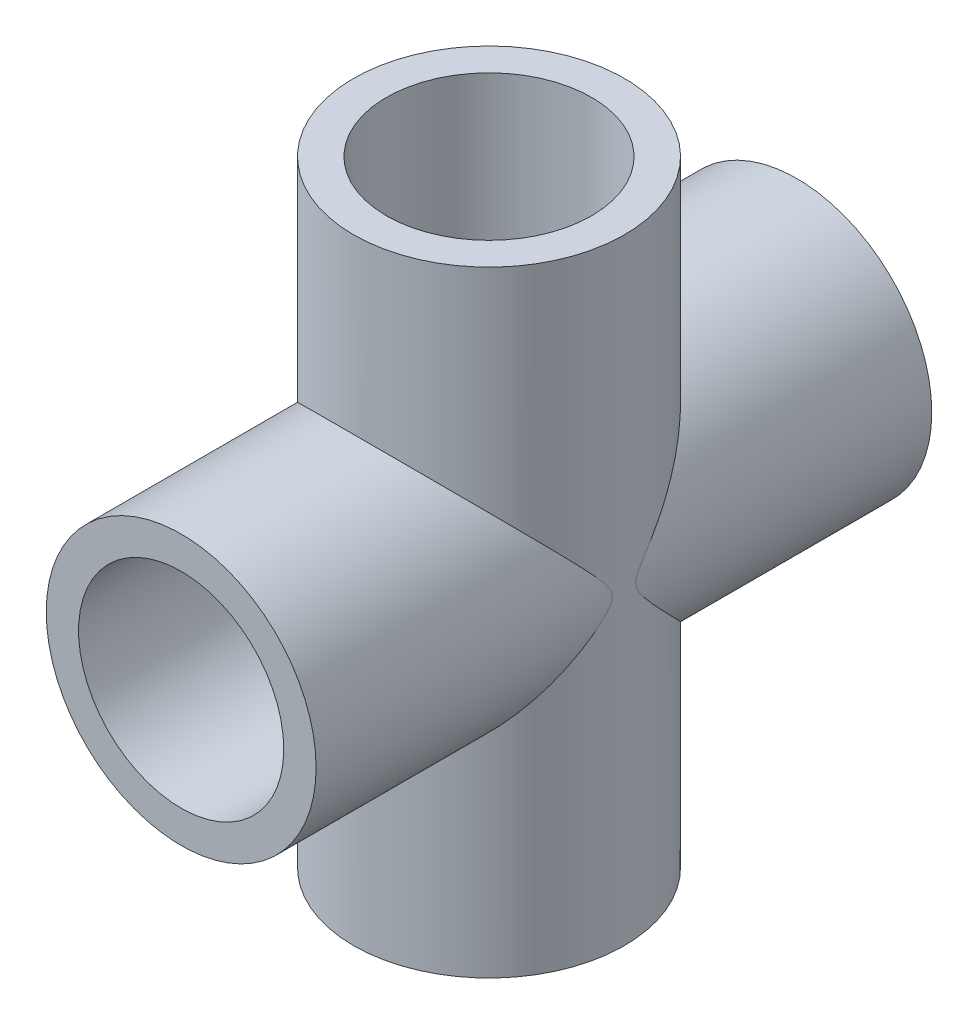
SolidWorks part; units mm, degrees
material "PVC Rigid"
ref_plane "Front Plane" through (0, 0, 0) normal (0, 0, 1) x (1, 0, 0)
ref_plane "Top Plane" through (0, 0, 0) normal (0, 1, 0) x (1, 0, 0)
ref_plane "Right Plane" through (0, 0, 0) normal (1, 0, 0) x (0, 0, -1)
sketch "Sketch1" plane through (0, 0, 0) normal (0, 0, 1) x (1, 0, 0)
  circle A0 centre (0, 0) radius 12.7
  circle A1 centre (0, 0) radius 16.7005
  dimension "D1" = 25.4
  dimension "D2" = 33.401
extrude "Boss-Extrude1" add sketch "Sketch1" along normal blind 76.2
sketch "Sketch2" plane through (0, 0, 0) normal (0, 1, 0) x (1, 0, 0)
  line L0 (-16.7005, -38.1) -> (16.7005, -38.1) construction
  line L1 (-16.7005, 0) -> (-16.7005, -76.2) construction
  line L2 (16.7005, -76.2) -> (16.7005, 0) construction
  circle A0 centre (0, -38.1) radius 16.764
  circle A1 centre (0, -38.1) radius 12.7
  dimension "D1" = 33.528
  dimension "D2" = 25.4
extrude "Boss-Extrude2" add sketch "Sketch2" along normal mid plane 76.2
sketch "Sketch5" plane through (0, 38.1, 0) normal (0, 1, 0) x (1, 0, 0)
  circle A0 centre (0, -38.1) radius 12.7
extrude "Cut-Extrude3" cut sketch "Sketch5" against normal up to next
sketch "Sketch6" plane through (0, 0, 0) normal (0, 0, -1) x (-1, 0, 0)
  circle A0 centre (0, 0) radius 12.7
  dimension "D1" = 25.4
extrude "Cut-Extrude4" cut sketch "Sketch6" against normal through all and the other way through all
sketch "Sketch7" plane through (0, -38.1, 0) normal (0, -1, 0) x (1, 0, 0)
  circle A0 centre (0, 38.1) radius 12.7
extrude "Cut-Extrude5" cut sketch "Sketch7" against normal through all
